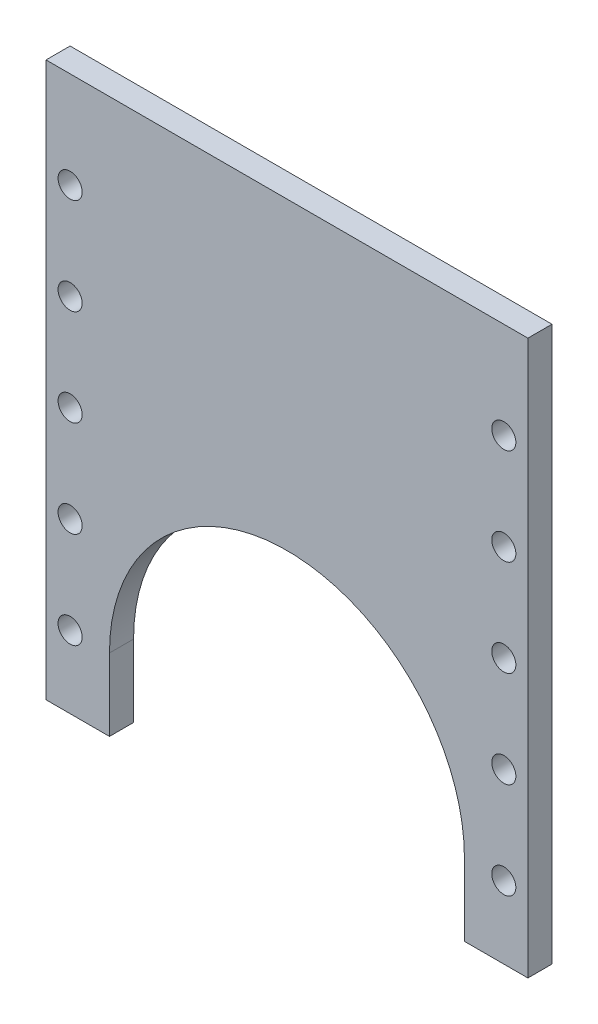
SolidWorks part; units mm, degrees
ref_plane "Front Plane" through (0, 0, 0) normal (0, 0, 1) x (1, 0, 0)
ref_plane "Top Plane" through (0, 0, 0) normal (0, 1, 0) x (1, 0, 0)
ref_plane "Right Plane" through (0, 0, 0) normal (1, 0, 0) x (0, 0, -1)
sketch "Sketch1" plane through (0, 0, 0) normal (0, 0, 1) x (1, 0, 0)
  line L0 (0, 79.2141) -> (0, 36.83) construction
  line L2 (-50, -15) -> (-50, 100)
  line L3 (-50, 100) -> (50, 100)
  line L4 (50, -15) -> (50, 100)
  line L5 (-45, 0) -> (46.5516, 0) construction
  line L6 (-50, -15) -> (-36.83, -15)
  line L7 (36.83, -15) -> (50, -15)
  line L10 (-36.83, 0) -> (-36.83, -15)
  line L11 (36.83, 0) -> (36.83, -15)
  circle A0 centre (-45, 0) radius 2.5
  circle A1 centre (45, 0) radius 2.5
  circle A2 centre (45, 20) radius 2.5
  circle A3 centre (45, 40) radius 2.5
  circle A4 centre (45, 60) radius 2.5
  circle A5 centre (45, 80) radius 2.5
  circle A6 centre (-45, 20) radius 2.5
  arc A7 (36.83, 0) -> (-36.83, 0) centre (0, 0) ccw
  circle A8 centre (-45, 40) radius 2.5
  circle A9 centre (-45, 60) radius 2.5
  circle A10 centre (-45, 80) radius 2.5
  dimension "D1" = 5
  dimension "D3" = 45
  dimension "D9" = 36.83
  dimension "D5" = 100
  dimension "D6" = 50
  dimension "D7" = 15
extrude "Boss-Extrude1" add sketch "Sketch1" along normal blind 5
